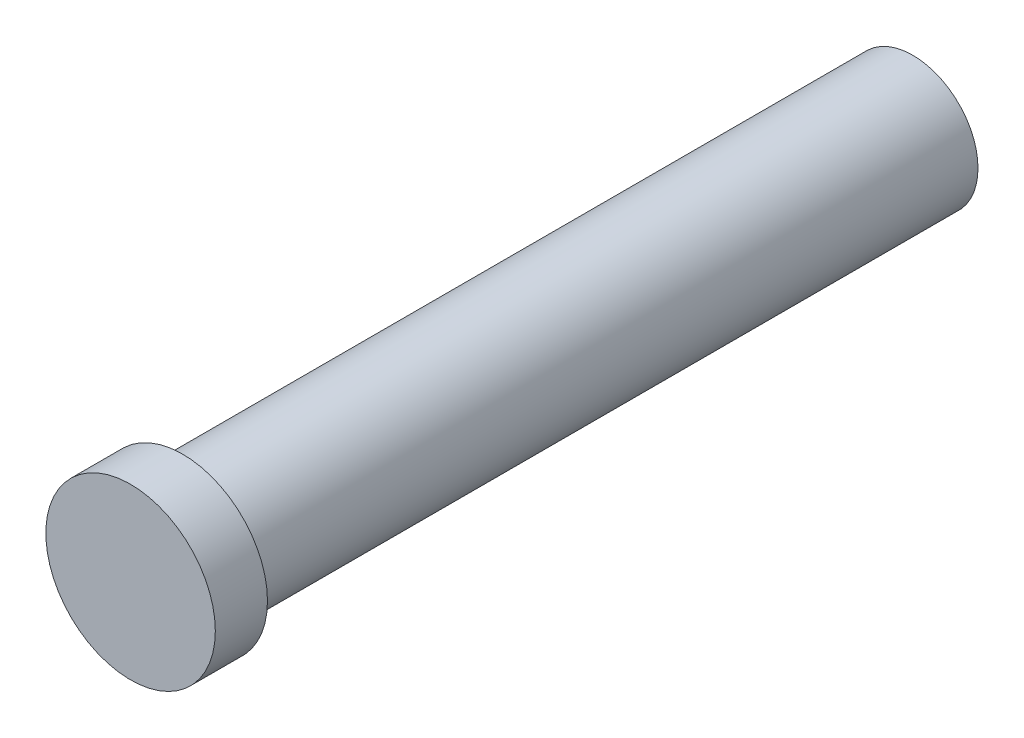
SolidWorks part; units mm, degrees
ref_plane "前视基准面" through (0, 0, 0) normal (0, 0, 1) x (1, 0, 0)
ref_plane "上视基准面" through (0, 0, 0) normal (0, 1, 0) x (1, 0, 0)
ref_plane "右视基准面" through (0, 0, 0) normal (1, 0, 0) x (0, 0, -1)
sketch "草图1" plane through (0, 0, 0) normal (0, 0, 1) x (1, 0, 0)
  circle A0 centre (0, 0) radius 5
  dimension "D1" = 10
extrude "凸台-拉伸1" add sketch "草图1" along normal blind 56
sketch "草图2" plane through (0, 0, 56) normal (0, 0, 1) x (1, 0, 0)
  circle A0 centre (0, 0) radius 6.5
  dimension "D1" = 13
extrude "凸台-拉伸2" add sketch "草图2" along normal blind 4
hole_wizard "M6 螺纹孔1" positions "草图3" profile "草图4" tap size "M6" standard "ISO"
sketch "草图3" plane through (0, 0, 0) normal (0, 0, -1) x (-1, 0, 0)
  point P0 (0, 0)
sketch "草图4" plane through (0, 0, 0) normal (1, 0, 0) x (0, 1, 0)
  line L0 (0, 0) -> (0, 16.5022)
  line L1 (0, 16.5022) -> (2.5, 15)
  line L2 (2.5, 15) -> (2.5, 0)
  line L5 (2.5, 0) -> (0, 0)
  line L10 (0, 16.5022) -> (-2.5, 15) construction
  line L11 (0, -6.35) -> (0, 107.95) construction
  dimension "螺纹孔钻头直径" = 5
  dimension "螺纹孔钻头深度" = 15
  dimension "导头角度" = 118
cosmetic thread "孔螺蚊线1" parameters "D1"=12, "D2"=6
